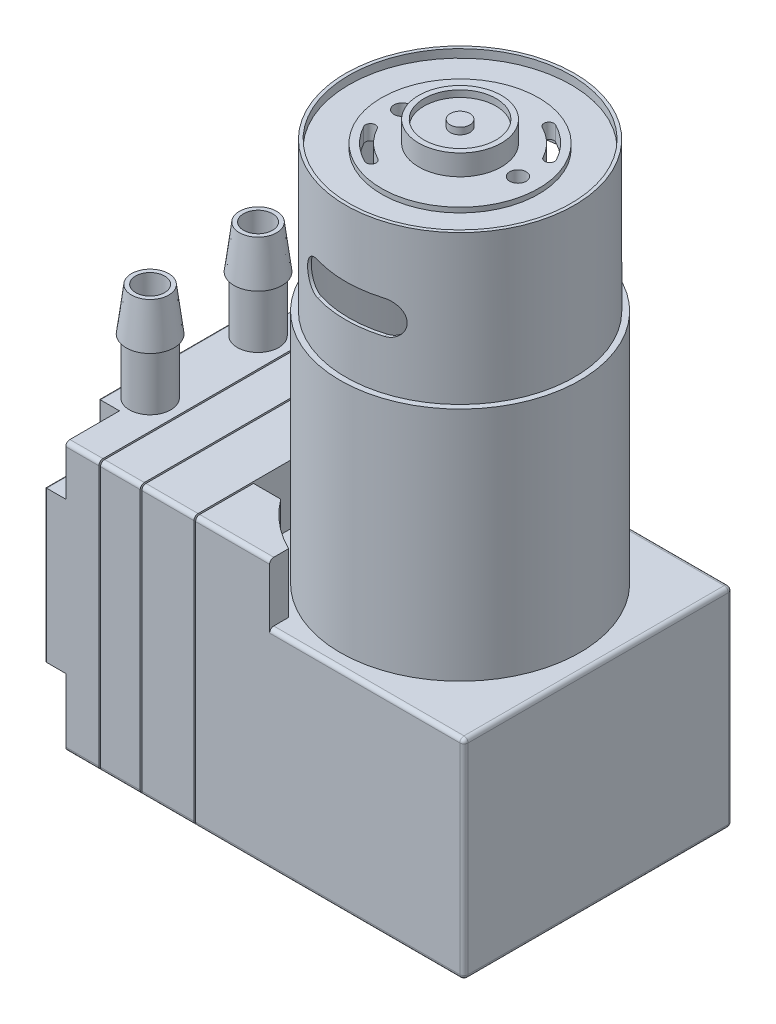
SolidWorks part; units mm, degrees
ref_plane "Plano frontal" through (0, 0, 0) normal (0, 0, 1) x (1, 0, 0)
ref_plane "Plano superior" through (0, 0, 0) normal (0, 1, 0) x (1, 0, 0)
ref_plane "Plano direito" through (0, 0, 0) normal (1, 0, 0) x (0, 0, -1)
sketch "Esboço1" plane through (0, 0, 0) normal (0, 1, 0) x (1, 0, 0)
  line L1 (0, 0) -> (50.65, 0)
  line L2 (0, 0) -> (0, 32.45)
  line L3 (0, 32.45) -> (50.65, 32.45)
  line L4 (50.65, 0) -> (50.65, 32.45)
  dimension "D1" = 50.65
  dimension "D2" = 32.45
extrude "Ressalto-extrusão1" add sketch "Esboço1" along normal blind 32.45
sketch "Esboço2" plane through (0, 0, 0) normal (0, 0, 1) x (1, 0, 0)
  line L1 (50.65, 32.45) -> (27.15, 32.45)
  line L2 (50.65, 32.45) -> (50.65, 25.25)
  line L3 (50.65, 25.25) -> (27.15, 25.25)
  line L4 (27.15, 32.45) -> (27.15, 25.25)
  dimension "D1" = 7.2
  dimension "D2" = 23.5
extrude "Corte-extrusão1" cut sketch "Esboço2" against normal blind 32.45
ref_plane "Plano1" through (18.2, 0, 0) normal (1, 0, 0) x (0, 0, -1)
sketch "Esboço3" plane through (18.2, 0, 0) normal (1, 0, 0) x (0, 0, -1)
  line L1 (0, 32.45) -> (32.45, 32.45)
  line L2 (0, 32.45) -> (0, 0)
  line L3 (0, 0) -> (32.45, 0)
  line L4 (32.45, 32.45) -> (32.45, 0)
  line L5 (0.2, 32.25) -> (32.25, 32.25)
  line L6 (0.2, 32.25) -> (0.2, 0.2)
  line L7 (0.2, 0.2) -> (32.25, 0.2)
  line L8 (32.25, 32.25) -> (32.25, 0.2)
  dimension "D1" = 0.2
  dimension "D2" = 0.2
  dimension "D3" = 0.2
extrude "Corte-extrusão2" cut sketch "Esboço3" against normal blind 0.2
ref_plane "Plano2" through (11.5, 0, 0) normal (-1, 0, 0) x (0, 0, 1)
sketch "Esboço4" plane through (11.5, 0, 0) normal (-1, 0, 0) x (0, 0, 1)
  line L4 (-0.2, 32.25) -> (-32.25, 32.25)
  line L5 (-32.25, 32.25) -> (-32.25, 0.2)
  line L6 (-32.25, 0.2) -> (-0.2, 0.2)
  line L7 (-0.2, 0.2) -> (-0.2, 32.25)
  line L8 (-0.2, 32.25) -> (-32.25, 32.25)
  line L9 (-32.25, 32.25) -> (-32.25, 0.2)
  line L10 (-32.25, 0.2) -> (-0.2, 0.2)
  line L11 (-0.2, 0.2) -> (-0.2, 32.25)
  line L12 (0, 32.45) -> (-32.45, 32.45)
  line L13 (-32.45, 32.45) -> (-32.45, 0)
  line L14 (-32.45, 0) -> (0, 0)
  line L15 (0, 0) -> (0, 32.45)
  line L16 (0, 32.45) -> (-32.45, 32.45)
  line L17 (-32.45, 32.45) -> (-32.45, 0)
  line L18 (-32.45, 0) -> (0, 0)
  line L19 (0, 0) -> (0, 32.45)
  dimension "D1" = 0
  dimension "D2" = 0
extrude "Corte-extrusão3" cut sketch "Esboço4" against normal blind 0.2
ref_plane "Plano3" through (6.5, 0, 0) normal (-1, 0, 0) x (0, 0, 1)
sketch "Esboço5" plane through (6.5, 0, 0) normal (-1, 0, 0) x (0, 0, 1)
  line L4 (0, 32.45) -> (-32.45, 32.45)
  line L5 (-32.45, 32.45) -> (-32.45, 0)
  line L6 (-32.45, 0) -> (0, 0)
  line L7 (0, 0) -> (0, 32.45)
  line L8 (0, 32.45) -> (-32.45, 32.45)
  line L9 (-32.45, 32.45) -> (-32.45, 0)
  line L10 (-32.45, 0) -> (0, 0)
  line L11 (0, 0) -> (0, 32.45)
  line L12 (-0.2, 32.25) -> (-32.25, 32.25)
  line L13 (-32.25, 32.25) -> (-32.25, 0.2)
  line L14 (-32.25, 0.2) -> (-0.2, 0.2)
  line L15 (-0.2, 0.2) -> (-0.2, 32.25)
  line L16 (-0.2, 32.25) -> (-32.25, 32.25)
  line L17 (-32.25, 32.25) -> (-32.25, 0.2)
  line L18 (-32.25, 0.2) -> (-0.2, 0.2)
  line L19 (-0.2, 0.2) -> (-0.2, 32.25)
  dimension "D1" = 0
  dimension "D2" = 0
extrude "Corte-extrusão4" cut sketch "Esboço5" against normal blind 0.2
sketch "Esboço6" plane through (0, 0, 0) normal (-1, 0, 0) x (0, 0, 1)
  line L0 (-32.45, 8.2) -> (-28.95, 8.2)
  line L1 (-32.45, 32.45) -> (-32.45, 0) construction
  line L2 (-25.95, 5.2) -> (-25.95, 0)
  line L3 (-32.45, 0) -> (0, 0) construction
  line L4 (-16.225, 0) -> (-16.225, 32.45) construction
  line L5 (-32.45, 32.45) -> (0, 32.45) construction
  line L6 (-25.95, 0) -> (-32.45, 0)
  line L7 (-32.45, 0) -> (-32.45, 8.2)
  line L8 (0, 0) -> (0, 8.2)
  line L9 (-6.5, 0) -> (0, 0)
  line L10 (-6.5, 5.2) -> (-6.5, 0)
  line L11 (0, 8.2) -> (-3.5, 8.2)
  line L12 (-32.45, 32.45) -> (-32.45, 26.45)
  line L13 (-32.45, 26.45) -> (-28.95, 26.45)
  line L14 (-25.95, 29.45) -> (-25.95, 32.45)
  line L15 (-25.95, 32.45) -> (-32.45, 32.45)
  line L16 (-6.5, 32.45) -> (0, 32.45)
  line L17 (-6.5, 29.45) -> (-6.5, 32.45)
  line L18 (0, 26.45) -> (-3.5, 26.45)
  line L19 (0, 32.45) -> (0, 26.45)
  arc A0 (-28.95, 8.2) -> (-25.95, 5.2) centre (-28.95, 5.2) cw
  arc A1 (-3.5, 8.2) -> (-6.5, 5.2) centre (-3.5, 5.2) ccw
  arc A2 (-28.95, 26.45) -> (-25.95, 29.45) centre (-28.95, 29.45) ccw
  arc A3 (-3.5, 26.45) -> (-6.5, 29.45) centre (-3.5, 29.45) cw
  point P27 (0, 0)
  dimension "D3" = 3
  dimension "D4" = 3
  dimension "D1" = 6.5
  dimension "D2" = 8.2
  dimension "D5" = 6
extrude "Corte-extrusão5" cut sketch "Esboço6" against normal blind 2.5
fillet "Filete1" radius 0.2 16 edges at (0, 2.6, -6.5) (0, 0, -16.225) (0, 2.6, -25.95) (0, 7.3213, -26.8287) (0, 8.2, -30.7) (0, 17.325, -32.45) (0, 26.45, -30.7) (0, 27.3287, -26.8287) (0, 30.95, -25.95) (0, 32.45, -16.225) (0, 30.95, -6.5) (0, 27.3287, -5.6213) (0, 26.45, -1.75) (0, 17.325, 0) (0, 8.2, -1.75) (0, 7.3213, -5.6213)
fillet "Filete2" radius 0.5 34 edges at (50.65, 0, -16.225) (50.65, 12.625, 0) (50.65, 25.25, -16.225) (50.65, 12.625, -32.45) (6.6, 0.2, -0.2) (11.6, 0.2, -0.2) (18.1, 0.2, -0.2) (34.425, 0, 0) (14.85, 0, 0) (9.1, 0, 0) (4.5, 0, 0) (18.1, 32.25, -0.2) (11.6, 32.25, -0.2) (6.6, 32.25, -0.2) (4.5, 32.45, 0) (9.1, 32.45, 0) (14.85, 32.45, 0) (22.675, 32.45, 0) (38.9, 25.25, 0) (38.9, 25.25, -32.45) (4.5, 0, -32.45) (6.6, 0.2, -32.25) (9.1, 0, -32.45) (11.6, 0.2, -32.25) (14.85, 0, -32.45) (18.1, 0.2, -32.25) (34.425, 0, -32.45) (6.6, 32.25, -32.25) (11.6, 32.25, -32.25) (18.1, 32.25, -32.25) (22.675, 32.45, -32.45) (14.85, 32.45, -32.45) (9.1, 32.45, -32.45) (4.5, 32.45, -32.45)
sketch "Esboço7" plane through (0, 25.25, 0) normal (0, 1, 0) x (1, 0, 0)
  line L0 (50.15, 16.225) -> (0.2, 16.225) construction
  line L1 (50.15, 0.5) -> (50.15, 31.95) construction
  line L2 (0.2, 25.95) -> (0.2, 6.5) construction
  line L5 (50.65, 31.95) -> (50.65, 0.5) construction
  circle A0 centre (33.95, 16.225) radius 15.5
  point P8 (34.3169, 16.225)
  dimension "D1" = 31
  dimension "D2" = 1.2
extrude "Corte-extrusão6" cut sketch "Esboço7" along normal through all
sketch "Esboço8" plane through (0, 32.45, 0) normal (0, 1, 0) x (1, 0, 0)
  line L0 (21.4941, 25.45) -> (18, 25.45)
  line L1 (18, 31.95) -> (18, 0.5) construction
  line L2 (18, 25.45) -> (18, 7)
  line L3 (18, 7) -> (21.4941, 7)
  line L4 (27.15, 0) -> (18.2, 0) construction
  arc A0 (27.15, 30.1537) -> (27.15, 2.2963) centre (33.95, 16.225) ccw construction
  arc A1 (21.4941, 25.45) -> (21.4941, 7) centre (33.95, 16.225) ccw
  point P7 (0, 0)
  dimension "D1" = 7
extrude "Corte-extrusão7" cut sketch "Esboço8" against normal up to surface (7.2 mm away) up to face at (33.3667, 25.25, -16.225)
sketch "Esboço9" plane through (0, 25.25, 0) normal (0, 1, 0) x (1, 0, 0)
  line L0 (20.2893, 18.35) -> (19.6066, 18.35)
  line L1 (20.2893, 14.1) -> (19.6066, 14.1)
  line L2 (20.2893, 18.35) -> (20.2893, 14.1) construction
  arc A0 (19.6066, 14.1) -> (19.6066, 18.35) centre (33.95, 16.225) ccw
  arc A1 (20.2893, 18.35) -> (20.2893, 14.1) centre (33.95, 16.225) ccw
  dimension "D1" = 29
  dimension "D2" = 27.65
  dimension "D3" = 4.25
extrude "Ressalto-extrusão2" add sketch "Esboço9" along normal blind 28.5
sketch "Esboço10" plane through (0, 53.75, 0) normal (0, 1, 0) x (1, 0, 0)
  circle A0 centre (33.95, 16.225) radius 13.825
extrude "Ressalto-extrusão3" add sketch "Esboço10" along normal blind 18
sketch "Esboço11" plane through (0, 71.75, 0) normal (0, 1, 0) x (1, 0, 0)
  circle A0 centre (33.95, 16.225) radius 13.425
  circle A1 centre (33.95, 16.225) radius 13.825 construction
  dimension "D1" = 0.4
extrude "Corte-extrusão8" cut sketch "Esboço11" against normal blind 1
sketch "Esboço12" plane through (0, 70.75, 0) normal (0, 1, 0) x (1, 0, 0)
  circle A0 centre (33.95, 16.225) radius 9.5
  dimension "D1" = 19
extrude "Ressalto-extrusão4" add sketch "Esboço12" along normal blind 0.6
sketch "Esboço13" plane through (0, 71.35, 0) normal (0, 1, 0) x (1, 0, 0)
  circle A0 centre (33.95, 16.225) radius 5
  circle A1 centre (33.95, 16.225) radius 4.35
  circle A2 centre (33.95, 16.225) radius 1.19
  dimension "D1" = 10
  dimension "D2" = 0.65
  dimension "D3" = 2.38
extrude "Ressalto-extrusão5" add sketch "Esboço13" along normal blind 2.5 contours A2 | A0 A1
sketch "Esboço14" plane through (0, 71.35, 0) normal (0, 1, 0) x (1, 0, 0)
  circle A0 centre (33.95, 16.225) radius 1.19 construction
  circle A1 centre (33.95, 16.225) radius 4.35
  circle A2 centre (33.95, 16.225) radius 4.35
  circle A3 centre (33.95, 16.225) radius 1.19
  dimension "D1" = 0
extrude "Ressalto-extrusão6" add sketch "Esboço14" along normal offset from surface (1.7 mm away) 0.8 up to face at (33.95, 73.85, -11.875)
sketch "Esboço15" plane through (0, 70.75, 0) normal (0, 1, 0) x (1, 0, 0)
  line L0 (26.95, 16.225) -> (40.95, 16.225) construction
  line L1 (33.95, 16.225) -> (39.5258, 21.9618) construction
  line L2 (33.95, 16.225) -> (31.3126, 18.7884) construction
  circle A0 centre (26.95, 16.225) radius 1
  circle A1 centre (40.95, 16.225) radius 1
  arc A2 (30.3521, 9.0797) -> (26.91, 12.4252) centre (33.95, 16.225) cw construction
  arc A3 (30.0822, 8.5438) -> (26.382, 12.1402) centre (33.95, 16.225) cw
  arc A4 (30.6219, 9.6156) -> (27.438, 12.7102) centre (33.95, 16.225) cw
  arc A5 (30.6219, 9.6156) -> (30.0822, 8.5438) centre (30.3521, 9.0797) cw
  arc A6 (26.382, 12.1402) -> (27.438, 12.7102) centre (26.91, 12.4252) cw
  arc A7 (40.99, 20.0248) -> (37.5479, 23.3703) centre (33.95, 16.225) ccw construction
  arc A8 (41.518, 20.3098) -> (37.8178, 23.9062) centre (33.95, 16.225) ccw
  arc A9 (40.462, 19.7398) -> (37.2781, 22.8344) centre (33.95, 16.225) ccw
  arc A10 (40.462, 19.7398) -> (41.518, 20.3098) centre (40.99, 20.0248) ccw
  arc A11 (37.8178, 23.9062) -> (37.2781, 22.8344) centre (37.5479, 23.3703) ccw
  arc A12 (40.99, 20.0248) -> (41.95, 16.225) centre (33.95, 16.225) cw construction
  point P4 (33.95, 16.225)
  point P5 (33.95, 16.225)
  point P6 (39.5258, 21.9618)
  point P22 (28.3742, 10.4882)
  dimension "D1" = 2
  dimension "D2" = 12
  dimension "D3" = 2.2
  dimension "D4" = 1.2
  dimension "D5" = 6
extrude "Corte-extrusão9" cut sketch "Esboço15" along normal through all and the other way blind 10.15
sketch "Esboço16" plane through (0, 0, 0) normal (0, 0, 1) x (1, 0, 0)
  line L0 (33.95, 71.75) -> (34.0283, 53.75) construction
  line L1 (47.775, 71.75) -> (20.125, 71.75) construction
  line L2 (48.45, 53.75) -> (19.6066, 53.75) construction
  line L3 (29.9935, 61.75) -> (37.9935, 61.75) construction
  line L4 (29.9935, 63.75) -> (37.9935, 63.75)
  line L5 (29.9935, 59.75) -> (37.9935, 59.75)
  line L6 (47.375, 71.75) -> (20.525, 71.75) construction
  arc A0 (29.9935, 63.75) -> (29.9935, 59.75) centre (29.9935, 61.75) ccw
  arc A1 (37.9935, 59.75) -> (37.9935, 63.75) centre (37.9935, 61.75) ccw
  point P8 (33.9935, 61.75)
  point P15 (0, 0)
  point P16 (33.9935, 61.75)
  dimension "D1" = 12
  dimension "D2" = 4
  dimension "D3" = 8
extrude "Corte-extrusão10" cut sketch "Esboço16" against normal through all
sketch "Esboço17" plane through (0, 25.25, 0) normal (0, 1, 0) x (1, 0, 0)
  circle A0 centre (33.95, 16.225) radius 13.425 construction
  circle A1 centre (33.95, 16.225) radius 13.425
extrude "Corte-extrusão11" cut sketch "Esboço17" along normal offset from surface (44.3 mm away) 1.2 up to face at (24.45, 70.75, -16.225)
ref_plane "Plano4" through (3, 0, 0) normal (-1, 0, 0) x (0, 0, 1)
sketch "Esboço18" plane through (3, 0, 0) normal (-1, 0, 0) x (0, 0, 1)
  line L0 (-9.7, 32.45) -> (-9.7, 40.2151) construction
  line L1 (-25.95, 32.45) -> (-6.5, 32.45) construction
  line L2 (-7.2, 32.45) -> (-7.2, 39.15)
  line L3 (-7.2, 39.15) -> (-6.8, 39.15)
  line L4 (-6.8, 39.15) -> (-7.45, 44.35)
  line L5 (-7.45, 44.35) -> (-7.95, 44.35)
  line L6 (-7.95, 44.35) -> (-7.95, 32.45)
  line L7 (-7.95, 32.45) -> (-7.2, 32.45)
  line L8 (-0.5, 32.45) -> (-6.5, 32.45) construction
  line L10 (0, 26.45) -> (0, 31.95) construction
  point P14 (-8.9325, 44.35)
  dimension "D1" = 6.7
  dimension "D2" = 5.2
  dimension "D3" = 4.5
  dimension "D4" = 5
  dimension "D5" = 5.8
  dimension "D6" = 7.2
  dimension "D7" = 3.5
revolve "Revolução1" add sketch "Esboço18" angle 360 about L0
ref_plane "Plano5" through (0, 0, -16.225) normal (0, 0, 1) x (1, 0, 0)
mirror "Espelhar1" about plane through (0, 0, -16.225) normal (0, 0, 1) of "Revolução1"
sketch "Esboço19" plane through (0, 0, 0) normal (-1, 0, 0) x (0, 0, 1)
  line L0 (-24, 28.2849) -> (-21.5, 28.2849)
  line L1 (-21.5, 28.2849) -> (-22.75, 30.45)
  line L2 (-22.75, 30.45) -> (-24, 28.2849)
  line L3 (-22.75, 30.45) -> (-22.75, 39.15) construction
  line L4 (-25.25, 39.15) -> (-20.25, 39.15) construction
  line L5 (-25.95, 32.45) -> (-6.5, 32.45) construction
  line L6 (-9.7, 44.35) -> (-9.7, 30.45) construction
  line L7 (-7.45, 44.35) -> (-11.95, 44.35) construction
  line L8 (-10.95, 30.45) -> (-8.45, 30.45)
  line L9 (-8.45, 30.45) -> (-9.7, 28.2849)
  line L10 (-9.7, 28.2849) -> (-10.95, 30.45)
  point P14 (-8.7175, 28.5291)
  point P16 (-9.7, 30.45)
  point P17 (0, 0)
  dimension "D1" = 2.5
  dimension "D2" = 2
  dimension "D3" = 2.5
extrude "Ressalto-extrusão7" add sketch "Esboço19" along normal blind 0.15
sketch "Esboço20" plane through (0, 0, 0) normal (0, -1, 0) x (1, 0, 0)
  line L1 (34.175, 0) -> (34.175, -16.225) construction
  line L2 (18.2, 0) -> (50.15, 0) construction
  line L3 (34.175, -16.225) -> (50.65, -16.225) construction
  line L4 (50.65, -0.5) -> (50.65, -31.95) construction
  circle A0 centre (34.175, -16.225) radius 1.7
  dimension "D1" = 3.4
extrude "Corte-extrusão12" cut sketch "Esboço20" against normal blind 2
